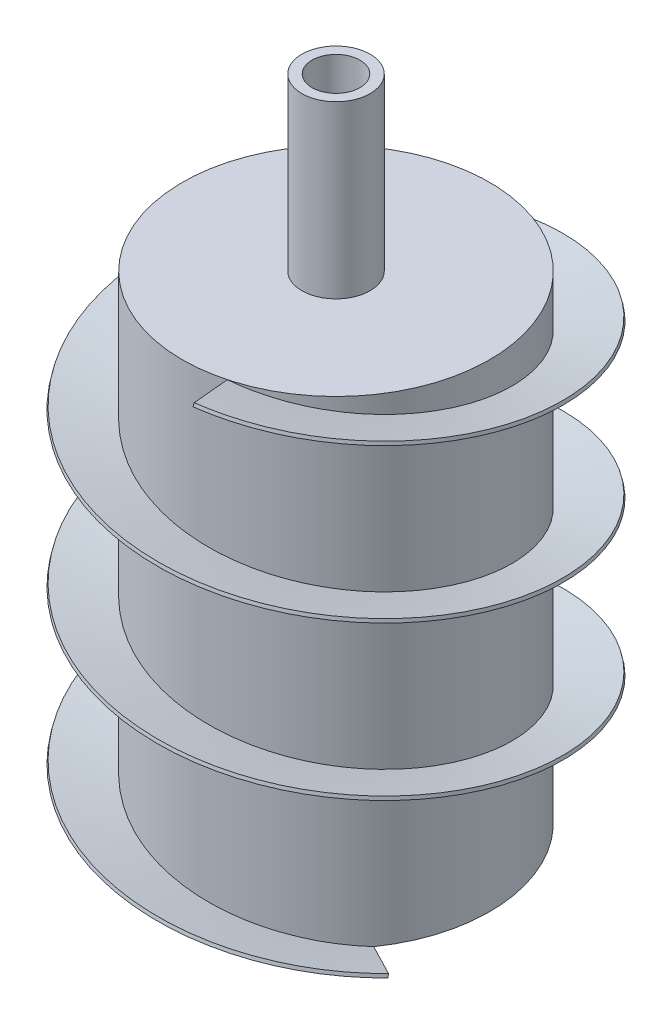
SolidWorks part; units mm, degrees
ref_plane "Front Plane" through (0, 0, 0) normal (0, 0, 1) x (1, 0, 0)
ref_plane "Top Plane" through (0, 0, 0) normal (0, 1, 0) x (1, 0, 0)
ref_plane "Right Plane" through (0, 0, 0) normal (1, 0, 0) x (0, 0, -1)
sketch "Sketch2" plane through (0, 0, 0) normal (0, 1, 0) x (1, 0, 0)
  circle A0 centre (0, 0) radius 45
extrude "Boss-Extrude1" add sketch "Sketch2" along normal blind 140
sketch "Sketch3" plane through (0, 0, 0) normal (0, 1, 0) x (1, 0, 0)
  circle A0 centre (0, 0) radius 45
curve "Helix/Spiral1" pitch 45 height 140 turns 3.1111
ref_plane "Plane1" through (11.6469, 140, 43.4667) normal (0.9539, -0.1572, -0.2556) x (-0.2861, -0.2201, -0.9326)
sketch "Sketch7" plane through (11.6469, 140, 43.4667) normal (0.9539, -0.1572, -0.2556) x (-0.2861, -0.2201, -0.9326)
  line L1 (0, 0) -> (-15, 0)
  line L2 (0, 0) -> (0, -1)
  line L3 (0, -1) -> (-15, -1)
  line L4 (-15, 0) -> (-15, -1)
  dimension "D1" = 15
  dimension "D2" = 1
sweep "Sweep2" add profiles "Sketch7" path "Helix/Spiral1"
sketch "Sketch9" plane through (0, 0, 0) normal (0, 1, 0) x (1, 0, 0)
  circle A0 centre (0, 0) radius 3.9
  circle A1 centre (0, 0) radius 3.5
extrude "Boss-Extrude2" add sketch "Sketch9" against normal blind 15
ref_plane "Plane3" through (0, 140, 0) normal (0, 1, 0) x (1, 0, 0)
sketch "Sketch10" plane through (0, 140, 0) normal (0, 1, 0) x (1, 0, 0)
  circle A0 centre (0, 0) radius 10
  circle A1 centre (0, 0) radius 7
extrude "Boss-Extrude3" add sketch "Sketch10" along normal blind 50
ref_plane "Plane4" through (0, 137, 0) normal (0, 1, 0) x (1, 0, 0)
sketch "Sketch19" plane through (0, 137, 0) normal (0, 1, 0) x (1, 0, 0)
  circle A0 centre (0, 0) radius 42
extrude "Cut-Extrude2" cut sketch "Sketch19" against normal blind 134
sketch "Sketch17" plane through (0, 0, 0) normal (0, 1, 0) x (1, 0, 0)
sketch "Sketch18" plane through (0, 0, 0) normal (0, 0, 1) x (1, 0, 0)
  line L0 (0, -278.8158) -> (0, 420.4035) construction
  line L1 (0, 0) -> (0, -9) construction
  line L2 (-1000, -9) -> (49000, -9) construction
  dimension "D1" = 9
ref_plane "Plane5" through (-3.9, 0, 0) normal (-1, 0, 0) x (0, 0, 1)
sketch "Sketch20" plane through (-3.9, 0, 0) normal (-1, 0, 0) x (0, 0, 1)
  line L0 (0, 0) -> (0, -9) construction
  line L1 (0, -278.8158) -> (0, 420.4035) construction
  circle A0 centre (0, -9) radius 1.5
extrude "Cut-Extrude4" cut sketch "Sketch20" against normal through all both
